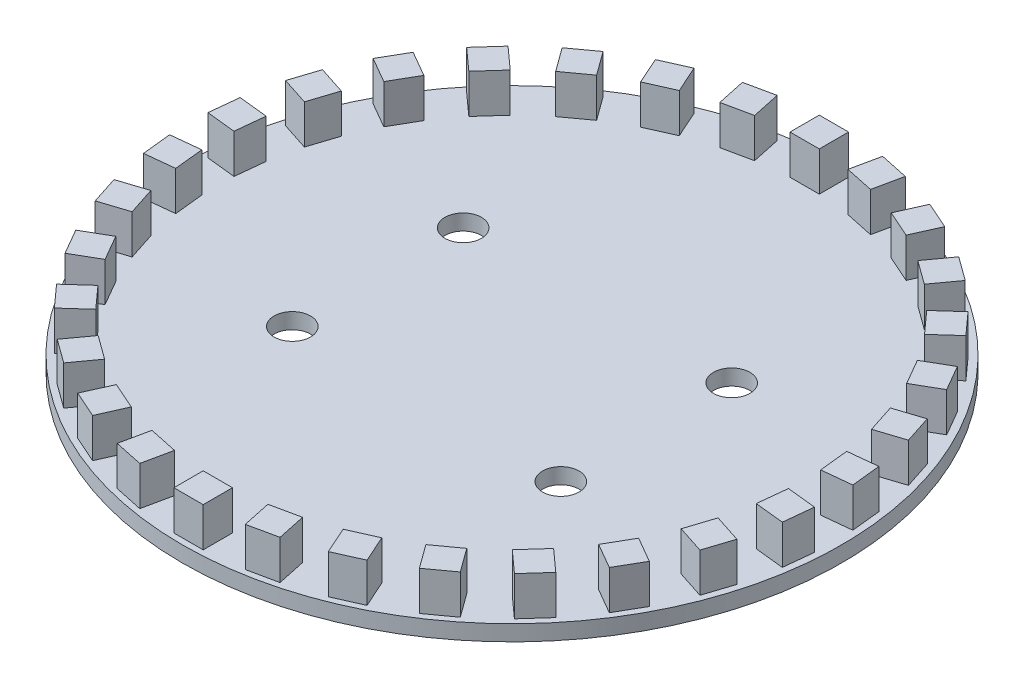
SolidWorks part; units mm, degrees
ref_plane "Front Plane" through (0, 0, 0) normal (0, 0, 1) x (1, 0, 0)
ref_plane "Top Plane" through (0, 0, 0) normal (0, 1, 0) x (1, 0, 0)
ref_plane "Right Plane" through (0, 0, 0) normal (1, 0, 0) x (0, 0, -1)
sketch "Sketch1" plane through (0, 0, 0) normal (0, 1, 0) x (1, 0, 0)
  circle A0 centre (0, 0) radius 34.29
  dimension "D1" = 68.58
extrude "Boss-Extrude1" add sketch "Sketch1" along normal blind 1.6383
sketch "Sketch3" plane through (0, 1.6383, 0) normal (0, 1, 0) x (1, 0, 0)
  line L0 (0, 0) -> (0, 33.4962) construction
  line L1 (0, 33.4962) -> (0, 30.4482) construction
  line L3 (1.524, 33.4963) -> (-1.524, 33.4963)
  line L4 (1.524, 33.4963) -> (1.524, 30.4482)
  line L5 (1.524, 30.4482) -> (-1.524, 30.4482)
  line L6 (-1.524, 33.4963) -> (-1.524, 30.4482)
  line L7 (1.524, 33.4963) -> (-1.524, 30.4482) construction
  line L8 (1.524, 30.4482) -> (-1.524, 33.4963) construction
  circle A0 centre (0, 0) radius 33.4962 construction
  point P3 (0, 31.9722)
  dimension "D1" = 66.9925
  dimension "D2" = 3.048
  dimension "D3" = 3.048
  dimension "D4" = 3.048
extrude "Boss-Extrude3" add sketch "Sketch3" along normal blind 4.0767
pattern_circular "CirPattern1" count 30 over 360 about axis through (0, 0, 0.0806) along (0, 1, 0) of "Boss-Extrude3"
sketch "hole positions" plane through (0, 0, 0) normal (0, 1, 0) x (1, 0, 0)
  line L1 (-13.97, 8.89) -> (13.97, 8.89) construction
  line L2 (-13.97, 8.89) -> (-13.97, -8.89) construction
  line L3 (-13.97, -8.89) -> (13.97, -8.89) construction
  line L4 (13.97, 8.89) -> (13.97, -8.89) construction
  line L5 (-13.97, 8.89) -> (13.97, -8.89) construction
  line L6 (-13.97, -8.89) -> (13.97, 8.89) construction
  point P0 (0, 0)
  dimension "D1" = 27.94
  dimension "D2" = 17.78
hole_wizard "#6 Clearance Hole1" positions "Sketch11" profile "Sketch12" hole size "#6" standard "ANSI Inch" end condition up to next
sketch "Sketch11" plane through (0, 0, 0) normal (0, -1, 0) x (-1, 0, 0)
  point P0 (13.97, -8.89)
  point P3 (13.97, 8.89)
  point P6 (-13.97, 8.89)
  point P9 (-13.97, -8.89)
sketch "Sketch12" plane through (-13.97, 0, 8.89) normal (1, 0, 0) x (0, 0, -1)
  line L0 (0, 0) -> (0, 1.6383)
  line L1 (0, 1.6383) -> (1.8986, 1.6383)
  line L2 (1.8986, 1.6383) -> (1.8986, 0)
  line L5 (1.8986, 0) -> (0, 0)
  line L11 (0, -6.35) -> (0, 107.95) construction
  dimension "Thru Hole Dia." = 3.7973
  dimension "Thru Hole Depth" = 1.6383
